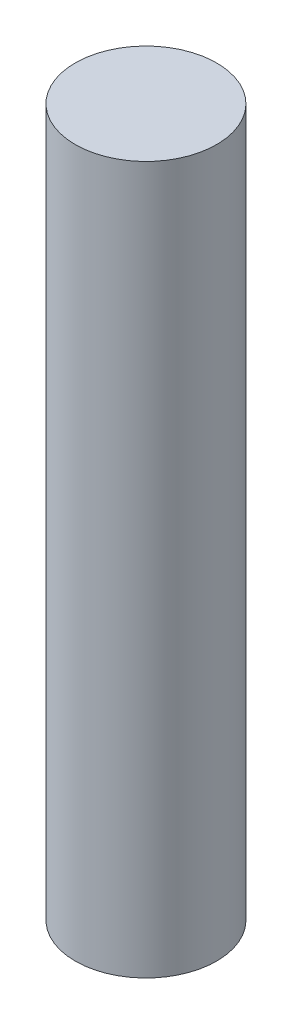
SolidWorks part; units mm, degrees
ref_plane "Front Plane" through (0, 0, 0) normal (0, 0, 1) x (1, 0, 0)
ref_plane "Top Plane" through (0, 0, 0) normal (0, 1, 0) x (1, 0, 0)
ref_plane "Right Plane" through (0, 0, 0) normal (1, 0, 0) x (0, 0, -1)
sketch "Sketch1" plane through (0, 0, 0) normal (0, 1, 0) x (1, 0, 0)
  circle A0 centre (0, 0) radius 17.78
  dimension "D1" = 35.56
extrude "Boss-Extrude1" add sketch "Sketch1" along normal blind 177.8
sketch "Sketch4" plane through (0, 0, 0) normal (0, -1, 0) x (1, 0, 0)
  circle A0 centre (0, 0) radius 3.175
  dimension "D1" = 6.35
extrude "Cut-Extrude1" cut sketch "Sketch4" against normal blind 152.4 contours A0
